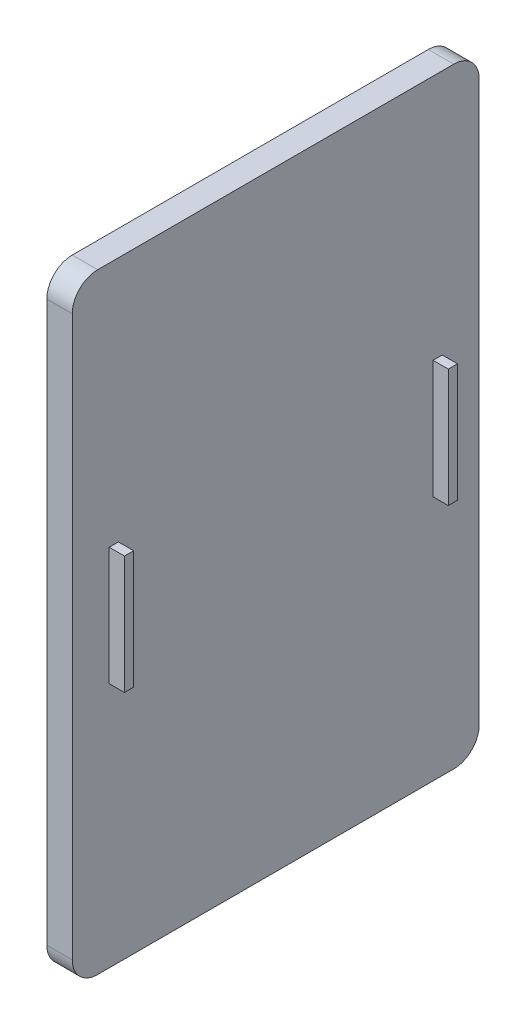
SolidWorks part; units mm, degrees
ref_plane "Front Plane" through (0, 0, 0) normal (0, 0, 1) x (1, 0, 0)
ref_plane "Top Plane" through (0, 0, 0) normal (0, 1, 0) x (1, 0, 0)
ref_plane "Right Plane" through (0, 0, 0) normal (1, 0, 0) x (0, 0, -1)
sketch "Sketch1" plane through (0, 0, 0) normal (1, 0, 0) x (0, 0, -1)
  line L1 (-40, 60) -> (40, 60)
  line L2 (-40, 60) -> (-40, -60)
  line L3 (-40, -60) -> (40, -60)
  line L4 (40, 60) -> (40, -60)
  line L5 (-40, 60) -> (40, -60) construction
  line L6 (-40, -60) -> (40, 60) construction
  point P0 (0, 0)
  dimension "D1" = 80
  dimension "D2" = 120
extrude "Boss-Extrude1" add sketch "Sketch1" along normal blind 5
fillet "Fillet1" radius 5 4 edges at (2.5, -60, 40) (2.5, -60, -40) (2.5, 60, -40) (2.5, 60, 40)
sketch "Sketch2" plane through (5, 0, 0) normal (1, 0, 0) x (0, 0, -1)
  line L1 (-32.7289, 11.6153) -> (-30.9245, 11.6153)
  line L2 (-32.7289, 11.6153) -> (-32.7289, -11.6153)
  line L3 (-32.7289, -11.6153) -> (-30.9245, -11.6153)
  line L4 (-30.9245, 11.6153) -> (-30.9245, -11.6153)
  line L5 (-32.7289, 11.6153) -> (-30.9245, -11.6153) construction
  line L6 (-32.7289, -11.6153) -> (-30.9245, 11.6153) construction
  point P0 (-31.8267, 0)
extrude "Boss-Extrude2" add sketch "Sketch2" along normal blind 3
mirror "Mirror1" about plane through (0, 0, 0) normal (0, 0, 1) of "Boss-Extrude2"
